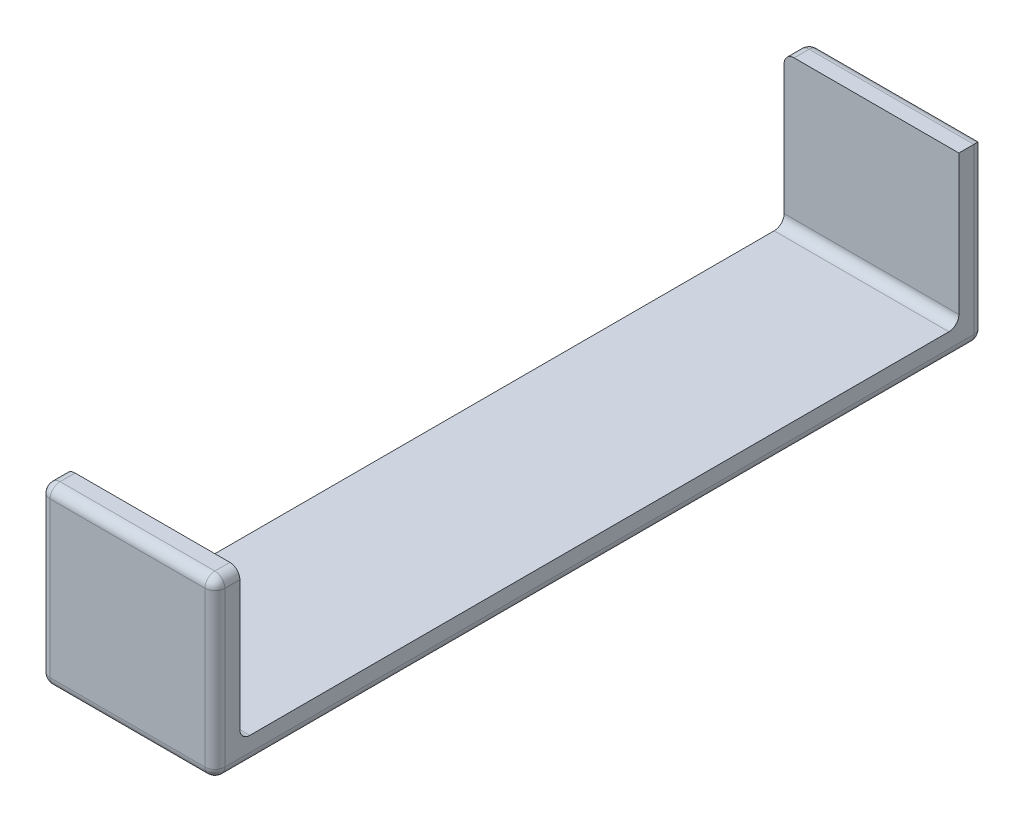
SolidWorks part; units mm, degrees
ref_plane "Plan de face" through (0, 0, 0) normal (0, 0, 1) x (1, 0, 0)
ref_plane "Plan de dessus" through (0, 0, 0) normal (0, 1, 0) x (1, 0, 0)
ref_plane "Plan de droite" through (0, 0, 0) normal (1, 0, 0) x (0, 0, -1)
sketch "Esquisse1" plane through (0, 0, 0) normal (0, 0, 1) x (1, 0, 0)
  line L1 (0, 0) -> (0, 17.5)
  line L2 (0, 17.5) -> (17.5, 17.5)
  line L3 (17.5, 17.5) -> (17.5, 0)
  line L4 (17.5, 0) -> (0, 0)
  dimension "D1" = 17.5
  dimension "D2" = 17.5
extrude "Boss.-Extru.1" add sketch "Esquisse1" along normal blind 77 contours L1 L2 L3 L4
sketch "Esquisse2" plane through (0, 0, 0) normal (-1, 0, 0) x (0, 0, 1)
  line L0 (0, 0) -> (0, 17.5) construction
  line L1 (2.5, 22.5) -> (74.5, 22.5)
  line L2 (2.5, 22.5) -> (2.5, 2.5)
  line L3 (2.5, 2.5) -> (74.5, 2.5)
  line L4 (74.5, 22.5) -> (74.5, 2.5)
  line L5 (77, 0) -> (77, 17.5) construction
  line L6 (77, 0) -> (0, 0) construction
  line L7 (77, 17.5) -> (0, 17.5) construction
  dimension "D1" = 2.5
  dimension "D2" = 2.5
  dimension "D3" = 2.5
  dimension "D4" = 5
extrude "Enlèv. mat.-Extru.1" cut sketch "Esquisse2" against normal through all
fillet "Congé1" radius 1 14 edges at (8.75, 17.5, 77) (0, 17.5, 1.25) (17.5, 8.75, 77) (8.75, 2.5, 2.5) (8.75, 2.5, 74.5) (8.75, 0, 77) (17.5, 8.75, 0) (8.75, 17.5, 0) (0, 8.75, 0) (8.75, 0, 0) (17.5, 0, 38.5) (0, 17.5, 75.75) (0, 0, 38.5) (0, 8.75, 77)
equation "\"74.5.00mm\"=73"
